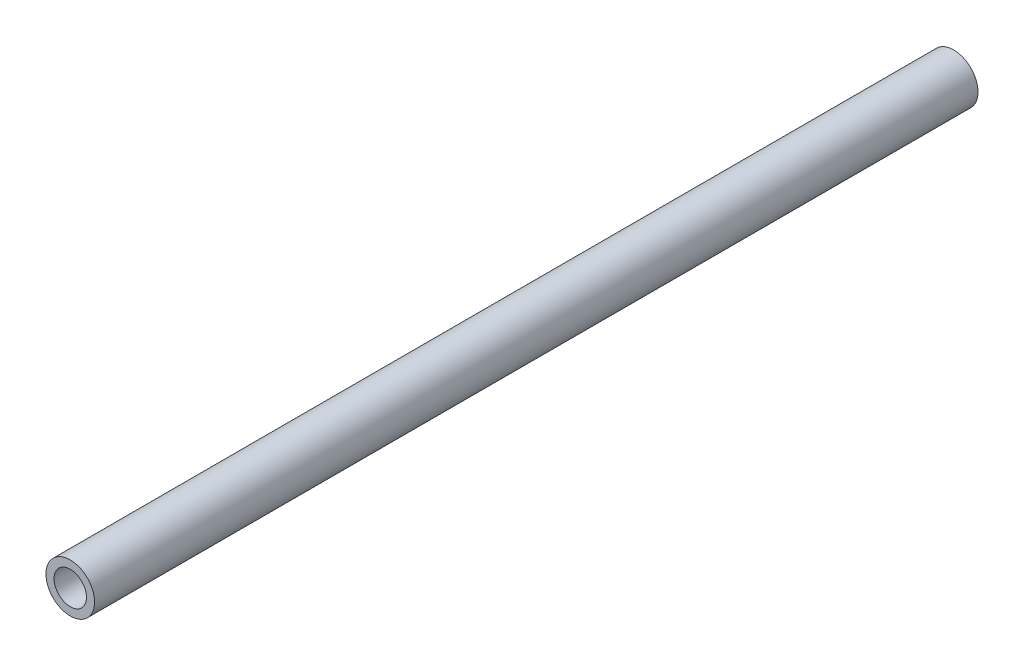
SolidWorks part; units mm, degrees
material "1060 Alloy"
ref_plane "Front Plane" through (0, 0, 0) normal (0, 0, 1) x (1, 0, 0)
ref_plane "Top Plane" through (0, 0, 0) normal (0, 1, 0) x (1, 0, 0)
ref_plane "Right Plane" through (0, 0, 0) normal (1, 0, 0) x (0, 0, -1)
sketch "Sketch1" plane through (0, 0, 0) normal (0, 0, 1) x (1, 0, 0)
  circle A0 centre (0, 0) radius 3
  circle A1 centre (0, 0) radius 2
  dimension "D1" = 6
  dimension "D2" = 4
extrude "Boss-Extrude1" add sketch "Sketch1" along normal blind 109
